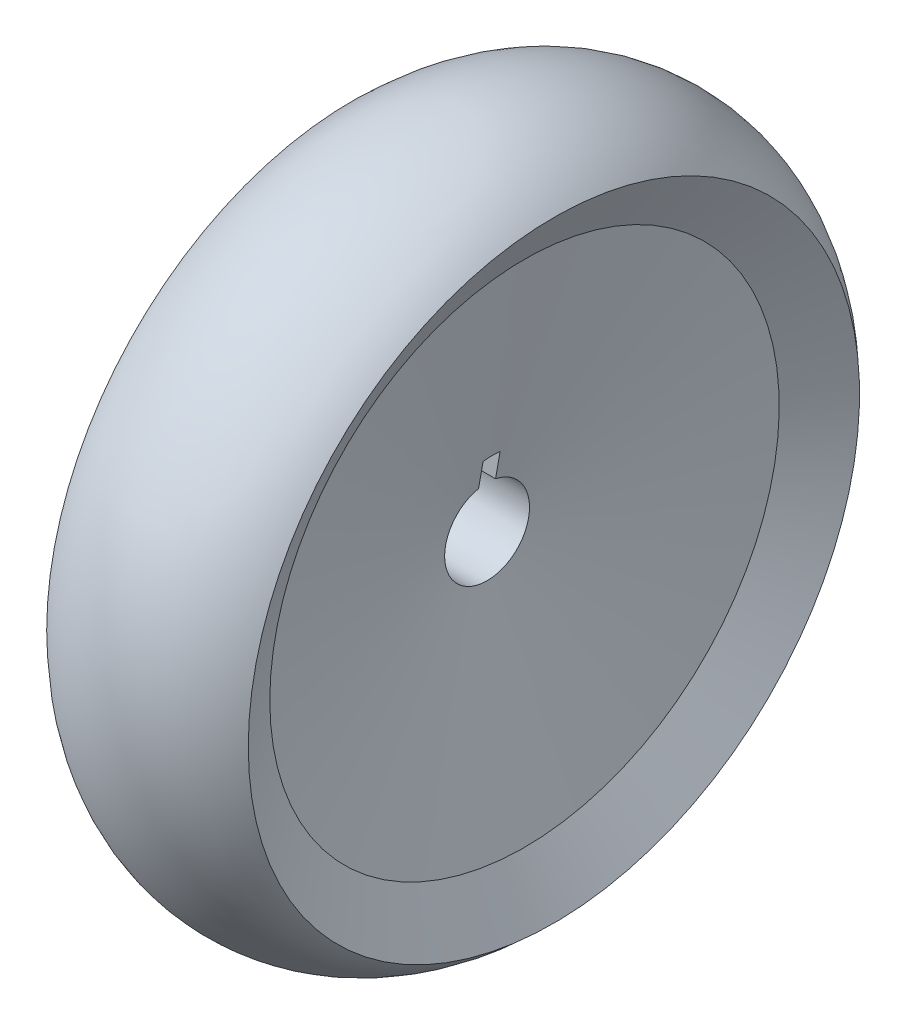
SolidWorks part; units mm, degrees
ref_plane "Front Plane" through (0, 0, 0) normal (0, 0, 1) x (1, 0, 0)
ref_plane "Top Plane" through (0, 0, 0) normal (0, 1, 0) x (1, 0, 0)
ref_plane "Right Plane" through (0, 0, 0) normal (1, 0, 0) x (0, 0, -1)
sketch "Sketch1" plane through (0, 0, 0) normal (0, 0, 1) x (1, 0, 0)
  line L0 (0, 10.3226) -> (0, -9.6774) construction
  line L1 (0, 0) -> (-10.0645, 0) construction
  line L2 (4, 0) -> (-4, 0)
  line L3 (-4, 0) -> (-8.4082, 25)
  line L4 (-8.4082, 25) -> (-11.8723, 31)
  line L5 (-4, 0) -> (-4, -5)
  line L6 (-4, -5) -> (0, -5)
  line L7 (-4, 0) -> (4, 0)
  line L8 (4, 0) -> (8.4082, 25)
  line L9 (8.4082, 25) -> (11.8723, 31)
  arc A0 (-11.8723, 31) -> (11.8723, 31) centre (0, 19.1752) cw
  dimension "D1" = 4
  dimension "D2" = 10
  dimension "D3" = 30
  dimension "D4" = 25
  dimension "D5" = 6
  dimension "D6" = 5
revolve "Revolve1" add sketch "Sketch1" angle 360 about L6
sketch "Sketch2" plane through (0, 0, 0) normal (1, 0, 0) x (0, 0, -1)
  line L1 (1, -5) -> (-1, -5)
  line L2 (1, -5) -> (1, 4.6786)
  line L3 (1, 4.6786) -> (-1, 4.6786)
  line L4 (-1, -5) -> (-1, 4.6786)
  circle A0 centre (0, -5) radius 8
  point P7 (0, 4.6786)
  dimension "D1" = 1
  dimension "D2" = 1
extrude "Cut-Extrude3" cut sketch "Sketch2" against normal blind 200.5 and the other way blind 20 contours L2 A0 L4 L1
